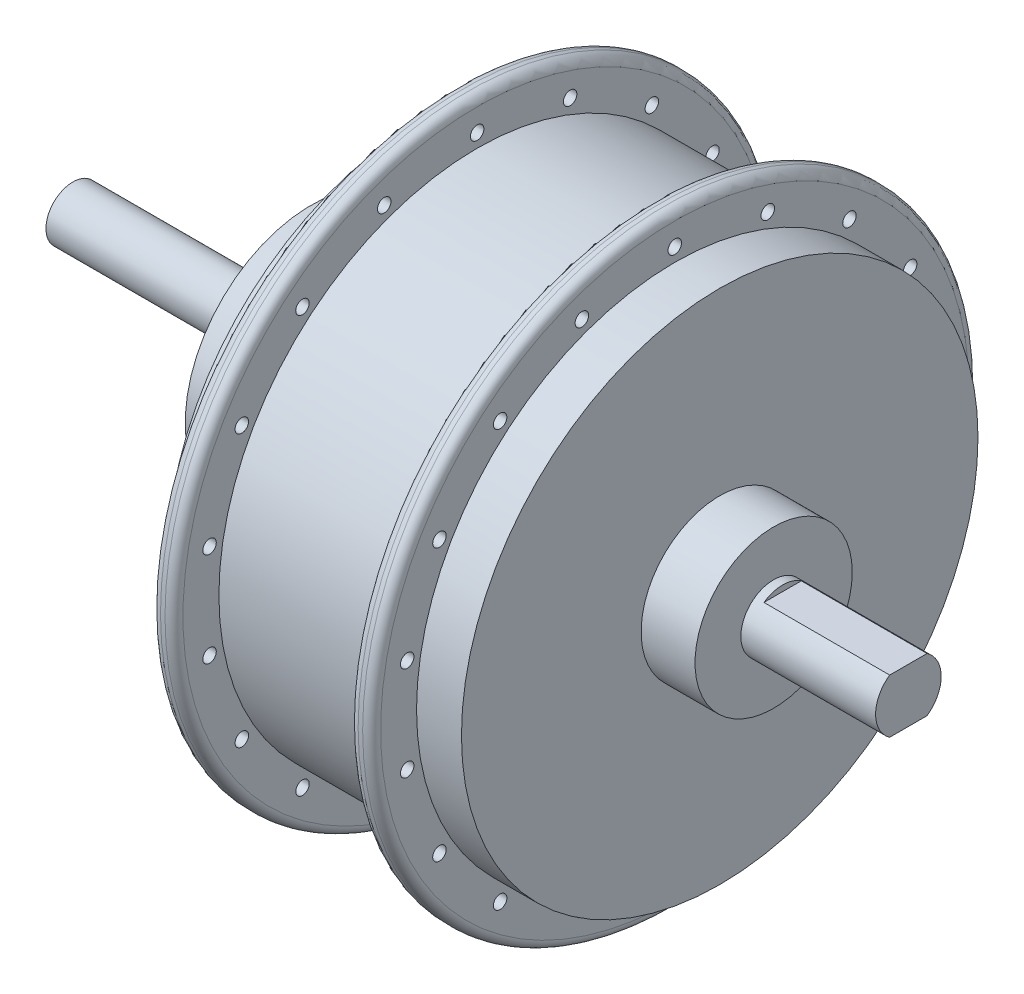
SolidWorks part; units mm, degrees
ref_plane "Спереди" through (0, 0, 0) normal (0, 0, 1) x (1, 0, 0)
ref_plane "Сверху" through (0, 0, 0) normal (0, 1, 0) x (1, 0, 0)
ref_plane "Справа" through (0, 0, 0) normal (1, 0, 0) x (0, 0, -1)
sketch "Эскиз1" plane through (0, 0, 0) normal (0, 0, 1) x (1, 0, 0)
  line L0 (27.6357, 0) -> (-114.9378, 0) construction
  line L1 (0, 0) -> (0, 7.3)
  line L2 (0, 7.3) -> (-30, 7.3)
  line L3 (-30, 7.3) -> (-30, 17.5)
  line L4 (-30, 17.5) -> (-42, 17.5)
  line L5 (-42, 17.5) -> (-42, 57.5)
  line L6 (-52, 67.5) -> (-57, 67.5)
  line L7 (-57, 67.5) -> (-57, 57.5)
  line L8 (-57, 57.5) -> (-96, 57.5)
  line L9 (-96, 57.5) -> (-96, 67.5)
  line L10 (-96, 67.5) -> (-101, 67.5)
  line L11 (-101, 67.5) -> (-101, 56)
  line L12 (-101, 56) -> (-109, 56)
  line L13 (-109, 56) -> (-109, 50)
  line L14 (-109, 50) -> (-121, 38)
  line L15 (-121, 38) -> (-121, 28)
  line L16 (-121, 28) -> (-133, 28)
  line L17 (-133, 28) -> (-133, 6)
  line L18 (-133, 6) -> (-186, 6)
  line L19 (-186, 6) -> (-186, 0)
  line L20 (-186, 0) -> (0, 0)
  line L21 (-52, 67.5) -> (-52, 57.5)
  line L22 (-52, 57.5) -> (-42, 57.5)
  point P24 (-101, 61.75)
  dimension "D1" = 14.6
  dimension "D2" = 35
  dimension "D3" = 135
  dimension "D4" = 10
  dimension "D5" = 112
  dimension "D6" = 100
  dimension "D7" = 76
  dimension "D8" = 56
  dimension "D9" = 12
  dimension "D10" = 59
  dimension "D11" = 5
  dimension "D12" = 103
  dimension "D13" = 12
  dimension "D14" = 53
  dimension "D15" = 10
  dimension "D16" = 8
  dimension "D17" = 12
  dimension "D18" = 12
  dimension "D19" = 30
  dimension "D20" = 67
  dimension "D21" = 79
  dimension "D22" = 10
  dimension "D23" = 5
revolve "Повернуть1" add sketch "Эскиз1" angle 360 about L0
fillet "Скругление1" radius 2 4 edges at (-101, 0, -67.5) (-96, 0, -67.5) (-57, 0, -67.5) (-52, 0, -67.5)
sketch "Эскиз2" plane through (-101, 0, 0) normal (-1, 0, 0) x (0, 0, 1)
  circle A0 centre (0, 60.5) radius 1.5
  circle A1 centre (20.6922, 56.8514) radius 1.5
  circle A2 centre (38.8887, 46.3457) radius 1.5
  circle A3 centre (52.3945, 30.25) radius 1.5
  circle A4 centre (59.5809, 10.5057) radius 1.5
  circle A5 centre (59.5809, -10.5057) radius 1.5
  circle A6 centre (52.3945, -30.25) radius 1.5
  circle A7 centre (38.8887, -46.3457) radius 1.5
  circle A8 centre (20.6922, -56.8514) radius 1.5
  circle A9 centre (0, -60.5) radius 1.5
  circle A10 centre (-20.6922, -56.8514) radius 1.5
  circle A11 centre (-38.8887, -46.3457) radius 1.5
  circle A12 centre (-52.3945, -30.25) radius 1.5
  circle A13 centre (-59.5809, -10.5057) radius 1.5
  circle A14 centre (-59.5809, 10.5057) radius 1.5
  circle A15 centre (-52.3945, 30.25) radius 1.5
  circle A16 centre (-38.8887, 46.3457) radius 1.5
  circle A17 centre (-20.6922, 56.8514) radius 1.5
  point P6 (0, 0)
  point P41 (0, 0)
  dimension "D2" = 3
  dimension "D1" = 59
  dimension "D3" = 18
extrude "Вырез-Вытянуть1" cut sketch "Эскиз2" against normal through all
sketch "Эскиз3" plane through (0, 0, 0) normal (1, 0, 0) x (0, 0, -1)
  line L1 (-26.3193, 6) -> (26.3193, 6)
  line L2 (-26.3193, 6) -> (-26.3193, -6)
  line L3 (-26.3193, -6) -> (26.3193, -6)
  line L4 (26.3193, 6) -> (26.3193, -6)
  line L5 (-26.3193, 6) -> (26.3193, -6) construction
  line L6 (-26.3193, -6) -> (26.3193, 6) construction
  point P0 (0, 0)
  dimension "D1" = 12
extrude "Вырез-Вытянуть2" cut sketch "Эскиз3" against normal blind 28 flip side to cut
